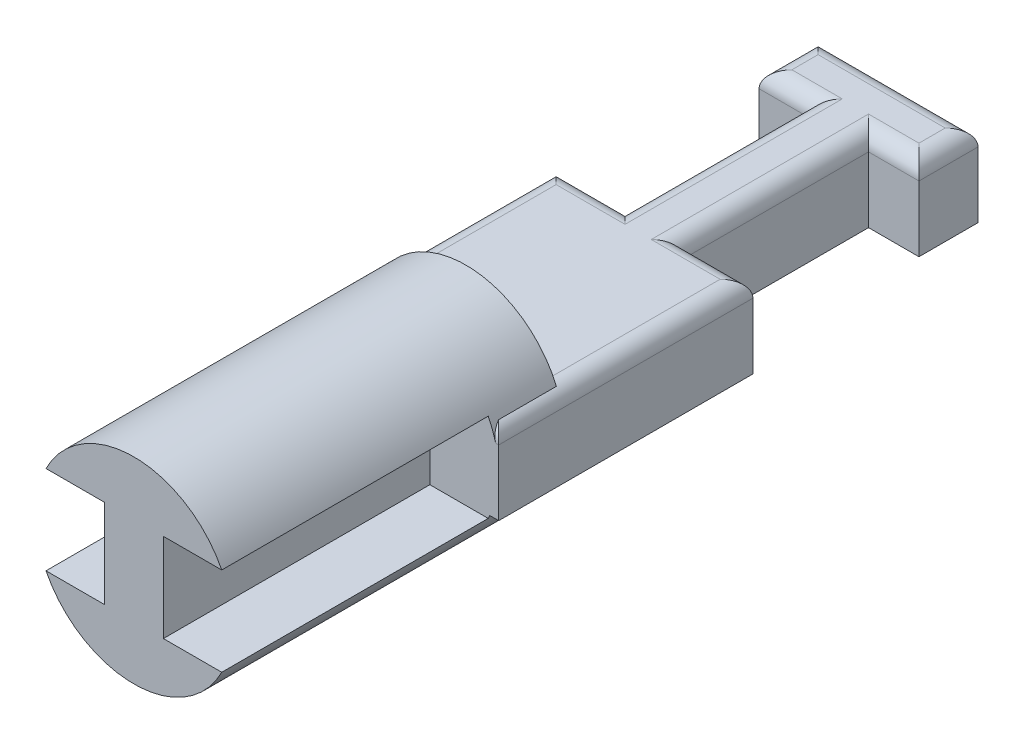
SolidWorks part; units mm, degrees
ref_plane "Front Plane" through (0, 0, 0) normal (0, 0, 1) x (1, 0, 0)
ref_plane "Top Plane" through (0, 0, 0) normal (0, 1, 0) x (1, 0, 0)
ref_plane "Right Plane" through (0, 0, 0) normal (1, 0, 0) x (0, 0, -1)
sketch "Sketch1" plane through (0, 0, 0) normal (0, 1, 0) x (1, 0, 0)
  line L1 (-0.9, -10.75) -> (0.9, -10.75)
  line L2 (-0.9, -10.75) -> (-0.9, 10.75)
  line L3 (-0.9, 10.75) -> (0.9, 10.75)
  line L4 (0.9, -10.75) -> (0.9, 10.75)
  line L5 (-2.4375, 12.55) -> (2.4375, 12.55)
  line L6 (-2.4375, 12.55) -> (-2.4375, 10.75)
  line L7 (-2.4375, 10.75) -> (2.4375, 10.75)
  line L8 (2.4375, 12.55) -> (2.4375, 10.75)
  line L9 (-3, 5.125) -> (3, 5.125)
  line L10 (-3, 5.125) -> (-3, -2.625)
  line L11 (-3, -2.625) -> (3, -2.625)
  line L12 (3, 5.125) -> (3, -2.625)
  point P8 (0, 10.75)
  point P9 (0, 10.75)
  point P11 (0.9, 0)
  point P16 (0, 5.125)
  dimension "D1" = 21.5
  dimension "D2" = 4.875
  dimension "D3" = 1.8
  dimension "D4" = 5.625
  dimension "6" = 6
  dimension "D6" = 7.75
extrude "Boss-Extrude1" add sketch "Sketch1" along normal mid plane 2.5 contours L1 L4 L3 L2 | L8 L5 L6 L7 L3 | L2 L9 L4 L3 | L10 L11 L2 L9 | L12 L9 L4 L11 | L11 L2 L1 L4
fillet "Fillet1" radius 0.5 16 edges at (0.9, 1.25, 6.6875) (-0.9, 1.25, 6.6875) (0, 1.25, 10.75) (-1.95, 1.25, 2.625) (1.95, 1.25, 2.625) (3, 1.25, -1.25) (1.95, 1.25, -5.125) (-3, 1.25, -1.25) (-1.95, 1.25, -5.125) (-0.9, 1.25, -7.9375) (0.9, 1.25, -7.9375) (1.6688, 1.25, -10.75) (2.4375, 1.25, -11.65) (0, 1.25, -12.55) (-2.4375, 1.25, -11.65) (-1.6688, 1.25, -10.75)
sketch "Sketch3" plane through (0, 0, 2.625) normal (0, 0, 1) x (1, 0, 0)
  line L0 (0.9, -1.25) -> (3, -1.25) construction
  line L1 (-0.9, -1.25) -> (0.9, -1.25) construction
  line L2 (-3, -1.25) -> (-0.9, -1.25) construction
  line L3 (0.9, -1.25) -> (3, -1.25)
  line L4 (-0.9, -1.25) -> (0.9, -1.25)
  line L5 (-3, -1.25) -> (-0.9, -1.25)
  line L6 (3, 0.75) -> (0.9, 0.75) construction
  line L7 (0.9, 0.75) -> (-0.9, 0.75) construction
  line L8 (-0.9, 0.75) -> (-3, 0.75) construction
  line L9 (3, 0.75) -> (0.9, 0.75)
  line L10 (0.9, 0.75) -> (-0.9, 0.75)
  line L11 (-0.9, 0.75) -> (-3, 0.75)
  circle A0 centre (0, 0) radius 3
  point P2 (0, -0.2885)
  point P4 (0, 0)
  line M3 (-0.9, 0.75) -> (-3, 0.75)
  dimension "D1" = 6
extrude "Boss-Extrude2" add sketch "Sketch3" against normal blind 2 contours L9 A0 L10 M3 | L5 A0 L3 L4
sketch "Sketch4" plane through (0, 0, 2.625) normal (0, 0, 1) x (1, 0, 0)
  line L0 (-2.6791, 1.35) -> (2.6791, 1.35)
  line L1 (2.6791, -1.35) -> (-2.6791, -1.35)
  line L2 (-0.4, 1.25) -> (0.4, 1.25) construction
  line L3 (-0.9, -1.25) -> (0.9, -1.25) construction
  line L4 (0.9, 0.75) -> (0.9, -1.25) construction
  line L5 (-0.9, 0.75) -> (-0.9, -1.25) construction
  line L6 (3, -1.25) -> (3, 0.75)
  line L7 (3, 0.75) -> (2.9047, 0.75)
  line L8 (-2.9047, 0.75) -> (-3, 0.75)
  line L9 (-3, 0.75) -> (-3, -1.25)
  line L10 (-3, -1.25) -> (-2.7272, -1.25)
  line L11 (2.7272, -1.25) -> (3, -1.25)
  line L12 (3, -1.25) -> (3, 0.75)
  line L13 (3, 0.75) -> (2.9047, 0.75)
  line L14 (-2.9047, 0.75) -> (-3, 0.75)
  line L15 (-3, 0.75) -> (-3, -1.25)
  line L16 (-3, -1.25) -> (-2.7272, -1.25)
  line L17 (2.7272, -1.25) -> (3, -1.25)
  line L18 (0.9, 0.75) -> (0.9, -1.25)
  line L19 (-0.9, 0.75) -> (-0.9, -1.25)
  line L20 (-0.9, -1.25) -> (-0.9, -1.35)
  line L21 (0.9, -1.25) -> (0.9, -1.35)
  line L22 (0.9, 0.75) -> (0.9, 1.35)
  line L23 (-0.9, 0.75) -> (-0.9, 1.35)
  circle A0 centre (0, 0) radius 3
  arc A2 (2.9047, 0.75) -> (-2.9047, 0.75) centre (0, 0) ccw
  arc A3 (-2.7272, -1.25) -> (2.7272, -1.25) centre (0, 0) ccw
  arc A4 (2.9047, 0.75) -> (-2.9047, 0.75) centre (0, 0) ccw
  arc A5 (-2.7272, -1.25) -> (2.7272, -1.25) centre (0, 0) ccw
  line M12 (0.9, -1.25) -> (-0.9, -1.25)
  line M13 (-0.9, -1.25) -> (-0.9, 0.75)
  arc M14 (-0.9, 0.75) -> (-0.4, 1.25) centre (-0.4, 0.75) cw
  line M15 (-0.4, 1.25) -> (0.4, 1.25)
  arc M16 (0.4, 1.25) -> (0.9, 0.75) centre (0.4, 0.75) cw
  line M17 (0.9, 0.75) -> (0.9, -1.25)
  arc M20 (2.9047, 0.75) -> (-2.9047, 0.75) centre (0, 0) ccw
  arc M24 (-2.7272, -1.25) -> (2.7272, -1.25) centre (0, 0) ccw
  dimension "D2" = 0.1
  dimension "D3" = 0.1
  dimension "D1" = 0
extrude "Boss-Extrude3" add sketch "Sketch4" along normal up to surface (8.125 mm away) contours L0 M20 | L1 M24 | M12 M17 M16 M15 M14 M13 | L23 L22 L0 M14 M15 M16 | L21 L20 L1 M12 up to face at (0, -0.25, 10.75)
sketch "Sketch5" plane through (0, 0, 0) normal (1, 0, 0) x (0, 0, -1)
  line L0 (12.55, 0.75) -> (12.55, -1.25) construction
  line L1 (12.55, 0.75) -> (12.55, -1.25)
  line L2 (12.55, -0.25) -> (13.2, -0.25)
  circle A0 centre (12.55, -0.25) radius 0.65
  dimension "D1" = 1.3
revolve "Revolve1" add sketch "Sketch5" angle 360 about L2
equation "\"D3@Sketch4\"=\"D2@Sketch4\""
